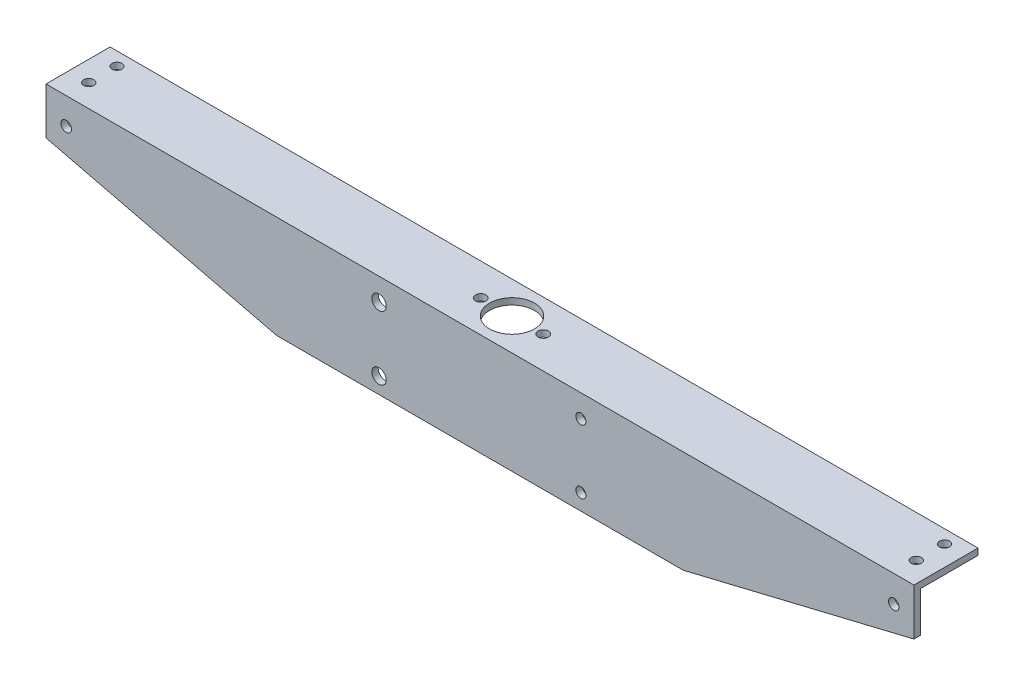
SolidWorks part; units mm, degrees
material "6063-T5"
ref_plane "Front Plane" through (0, 0, 0) normal (0, 0, 1) x (1, 0, 0)
ref_plane "Top Plane" through (0, 0, 0) normal (0, 1, 0) x (1, 0, 0)
ref_plane "Right Plane" through (0, 0, 0) normal (1, 0, 0) x (0, 0, -1)
sketch "Sketch1" plane through (0, 0, 0) normal (1, 0, 0) x (0, 0, -1)
  line L0 (0, 0) -> (31.75, 0)
  line L1 (31.75, 0) -> (31.75, -3.175)
  line L2 (31.75, -3.175) -> (3.175, -3.175)
  line L3 (3.175, -3.175) -> (3.175, -50.8)
  line L4 (3.175, -50.8) -> (0, -50.8)
  line L5 (0, -50.8) -> (0, 0)
  dimension "D1" = 31.75
  dimension "D2" = 3.175
  dimension "D3" = 3.175
  dimension "D4" = 50.8
extrude "Boss-Extrude1" add sketch "Sketch1" along normal mid plane 430
sketch "Sketch2" plane through (0, 0, -3.175) normal (0, 0, -1) x (-1, 0, 0)
  line L0 (0, 0) -> (0, -57.8721) construction
  line L1 (-215, -50.8) -> (215, -50.8) construction
  line L3 (-215, -3.175) -> (215, -3.175) construction
  circle A0 centre (-50, -11.175) radius 2.5
  circle A1 centre (50, -11.175) radius 3.57
  circle A2 centre (50, -42.8) radius 3.57
  circle A3 centre (-50, -42.8) radius 2.5
  dimension "D1" = 5
  dimension "D2" = 5
  dimension "D3" = 7.14
  dimension "D4" = 7.14
  dimension "D7" = 8
  dimension "D9" = 8
  dimension "D5" = 50
  dimension "D6" = 50
extrude "Cut-Extrude1" cut sketch "Sketch2" against normal through all
sketch "Sketch3" plane through (0, 0, -3.175) normal (0, 0, -1) x (-1, 0, 0)
  line L0 (215, -50.8) -> (100.7, -50.8)
  line L1 (-215, -50.8) -> (215, -50.8) construction
  line L2 (100.7, -50.8) -> (215, -23.175)
  line L3 (215, -50.8) -> (215, -3.175) construction
  line L4 (215, -23.175) -> (215, -50.8)
  line L5 (-215, -23.175) -> (-215, -50.8)
  line L6 (0, 0) -> (0, -50.8) construction
  line L7 (-100.7, -50.8) -> (-215, -23.175)
  line L8 (-215, -50.8) -> (-100.7, -50.8)
  dimension "D1" = 20
  dimension "D2" = 114.3
extrude "Cut-Extrude2" cut sketch "Sketch3" against normal blind 3.175
sketch "Sketch4" plane through (0, 0, 0) normal (0, 1, 0) x (1, 0, 0)
  line L0 (0, 0) -> (0, 31.75) construction
  line L1 (215, 31.75) -> (-215, 31.75) construction
  line L2 (-215, 31.75) -> (-215, 0) construction
  line L4 (215, 0) -> (-215, 0) construction
  circle A0 centre (-205, 11.176) radius 2.5
  circle A1 centre (-205, 25.176) radius 2.5
  circle A2 centre (205, 25.176) radius 2.5
  circle A3 centre (205, 11.176) radius 2.5
  dimension "D1" = 5
  dimension "D2" = 5
  dimension "D3" = 10
  dimension "D4" = 11.176
  dimension "D5" = 14
extrude "Cut-Extrude3" cut sketch "Sketch4" against normal blind 3.175
sketch "Sketch5" plane through (0, -3.175, 0) normal (0, -1, 0) x (1, 0, 0)
  line L0 (215, 0) -> (-215, 0) construction
  circle A0 centre (0, -15.875) radius 19.05 construction
  circle A1 centre (0, -15.875) radius 11.1125
  dimension "D1" = 22.225
  dimension "D2" = 38.1
  dimension "D3" = 15.875
extrude "Cut-Extrude4" cut sketch "Sketch5" against normal up to next
sketch "Sketch6" plane through (0, 0, 0) normal (0, 0, 1) x (1, 0, 0)
  line L0 (215, 0) -> (215, -23.175) construction
  line L1 (215, 0) -> (-215, 0) construction
  line L2 (0, 0) -> (0, -50.8) construction
  line L3 (100.7, -50.8) -> (-100.7, -50.8) construction
  circle A0 centre (205, -13.175) radius 2.6
  circle A1 centre (-205, -13.175) radius 2.6
  dimension "D1" = 5.2
  dimension "D3" = 13.175
  dimension "D2" = 10
extrude "Cut-Extrude5" cut sketch "Sketch6" against normal up to surface (3.175 mm away) up to face at (50, -40.3, -3.175)
sketch "Sketch7" plane through (0, 0, 0) normal (0, 1, 0) x (1, 0, 0)
  circle A0 centre (15.5, 15.875) radius 2.6
  circle A1 centre (-15.5, 15.875) radius 2.6
  dimension "D1" = 5.2
extrude "Cut-Extrude6" cut sketch "Sketch7" against normal up to surface (3.175 mm away) up to face at (0, -3.175, -26.9875)
equation "\"D2@Sketch2\"=\"D1@Sketch2\""
equation "\"D4@Sketch2\"=\"D3@Sketch2\""
equation "\"D2@Sketch4\" = \"D1@Sketch4\""
